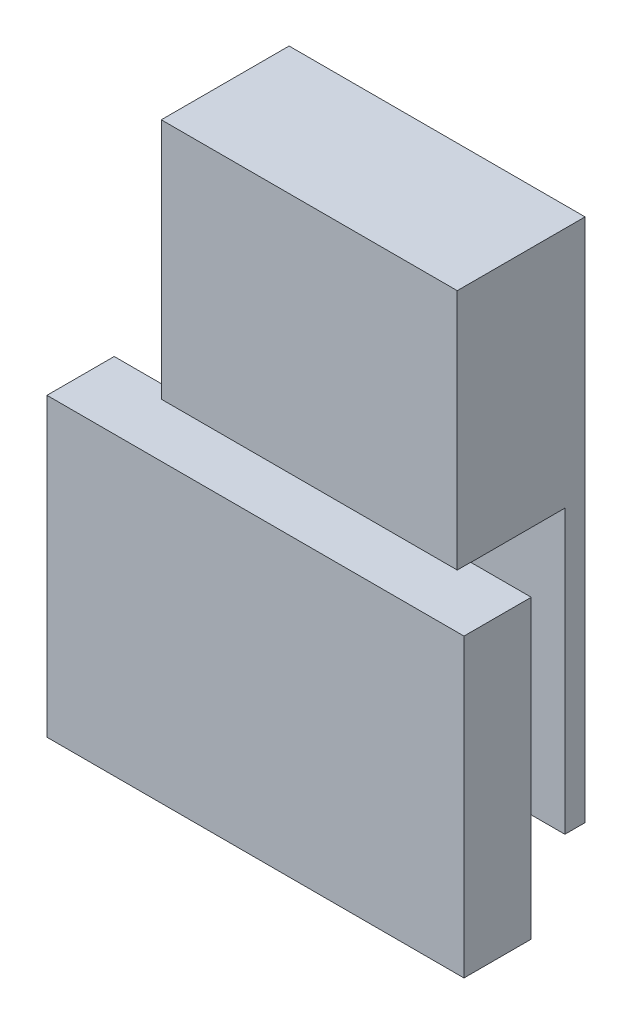
SolidWorks part; units mm, degrees
ref_plane "Front" through (0, 0, 0) normal (0, 0, 1) x (1, 0, 0)
ref_plane "Top" through (0, 0, 0) normal (0, 1, 0) x (1, 0, 0)
ref_plane "Right" through (0, 0, 0) normal (1, 0, 0) x (0, 0, -1)
sketch "Sketch1" plane through (0, 0, 0) normal (0, 0, 1) x (1, 0, 0)
  line L1 (27.94, -49.53) -> (-27.94, -49.53)
  line L2 (27.94, -49.53) -> (27.94, 49.53)
  line L3 (27.94, 49.53) -> (-27.94, 49.53)
  line L4 (-27.94, -49.53) -> (-27.94, 49.53)
  line L5 (27.94, -49.53) -> (-27.94, 49.53) construction
  line L6 (27.94, 49.53) -> (-27.94, -49.53) construction
  point P0 (0, 0)
  dimension "D1" = 99.06
  dimension "D2" = 55.88
extrude "Boss-Extrude1" add sketch "Sketch1" along normal blind 3.81
sketch "Sketch2" plane through (0, 0, 3.81) normal (0, 0, 1) x (1, 0, 0)
  line L0 (27.94, -49.53) -> (27.94, 49.53) construction
  line L1 (-27.94, 49.53) -> (27.94, 49.53)
  line L2 (-27.94, 49.53) -> (-27.94, 3.81)
  line L3 (-27.94, 3.81) -> (27.94, 3.81)
  line L4 (27.94, 49.53) -> (27.94, 3.81)
  dimension "D1" = 45.72
extrude "Boss-Extrude2" add sketch "Sketch2" along normal blind 20.32
sketch "Sketch3" plane through (0, 3.81, 0) normal (0, -1, 0) x (1, 0, 0)
  line L0 (27.94, 24.13) -> (27.94, 3.81) construction
  line L1 (-27.94, 24.13) -> (27.94, 24.13)
  line L2 (-27.94, 24.13) -> (-27.94, 21.59)
  line L3 (-27.94, 21.59) -> (27.94, 21.59)
  line L4 (27.94, 24.13) -> (27.94, 21.59)
  dimension "D1" = 2.54
extrude "Boss-Extrude3" add sketch "Sketch3" along normal blind 55.88
sketch "Sketch4" plane through (0, 0, 24.13) normal (0, 0, 1) x (1, 0, 0)
  line L0 (-39.37, -52.07) -> (39.37, -52.07)
  line L3 (-39.37, -52.07) -> (39.37, -52.07)
  line L4 (-39.37, -52.07) -> (-39.37, 3.8418)
  line L5 (-39.37, 3.8418) -> (39.37, 3.8418)
  line L6 (39.37, -52.07) -> (39.37, 3.8418)
  line M2 (-27.94, 49.53) -> (-27.94, -52.07)
  line M3 (-27.94, -52.07) -> (27.94, -52.07)
  line M4 (27.94, -52.07) -> (27.94, 49.53)
  dimension "D1" = 78.74
  dimension "D2" = 39.37
extrude "Boss-Extrude4" add sketch "Sketch4" along normal blind 10.16 and the other way blind 2.54 contours L5 L4 L0 M2 | L5 M2 M3 M4 | L0 L6 L5 M4
